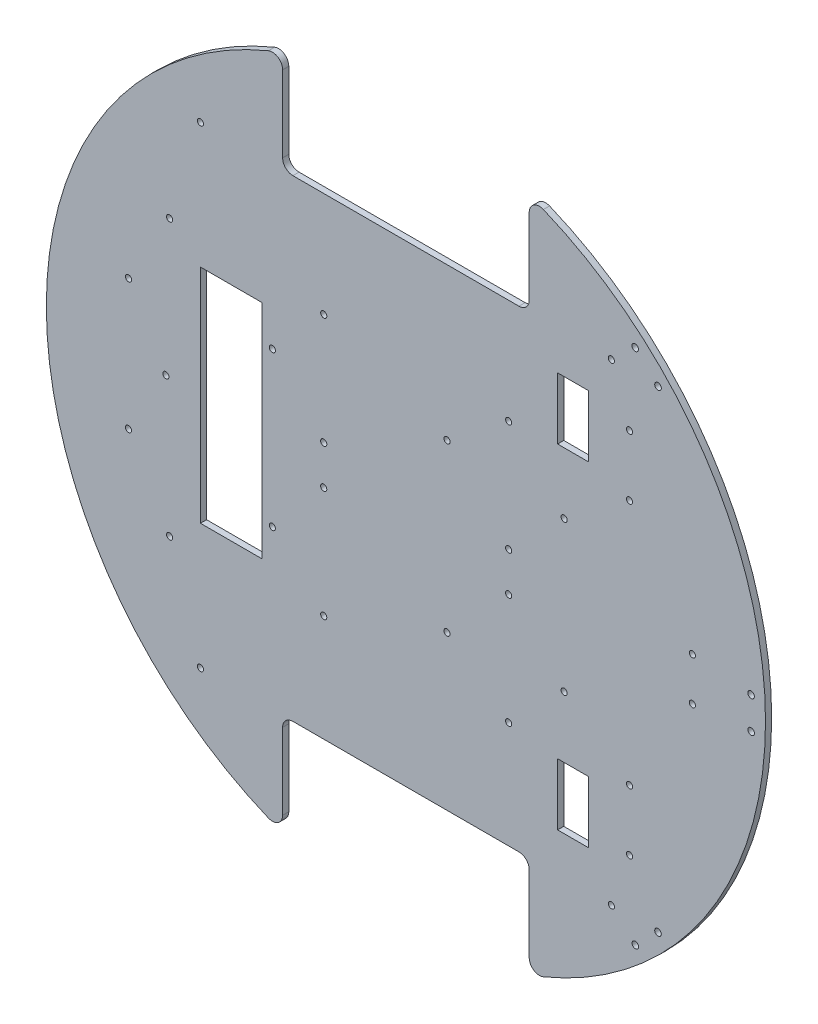
SolidWorks part; units mm, degrees
material "ｱｸﾘﾙ (中-上級の耐衝撃性)"
ref_plane "正面" through (0, 0, 0) normal (0, 0, 1) x (1, 0, 0)
ref_plane "平面" through (0, 0, 0) normal (0, 1, 0) x (1, 0, 0)
ref_plane "右側面" through (0, 0, 0) normal (1, 0, 0) x (0, 0, -1)
sketch "ｽｹｯﾁ1" plane through (0, 0, 0) normal (0, 0, 1) x (1, 0, 0)
  circle A0 centre (0, 0) radius 175
  dimension "D1" = 350
extrude "ﾎﾞｽ - 押し出し1" add sketch "ｽｹｯﾁ1" along normal blind 3
sketch "ｽｹｯﾁ2" plane through (0, 0, 3) normal (0, 0, 1) x (1, 0, 0)
  line L0 (0, 0) -> (175, 0)
  line L1 (0, 0) -> (-175, 0)
  line L2 (0, 0) -> (0, 115)
  line L3 (0, 0) -> (0, -115)
  line L4 (0, 115) -> (60, 115)
  line L5 (0, 115) -> (0, 175)
  line L6 (0, 175) -> (60, 175)
  line L7 (60, 115) -> (60, 175)
  line L8 (0, 115) -> (-60, 115)
  line L9 (0, 115) -> (0, 175)
  line L10 (0, 175) -> (-60, 175)
  line L11 (-60, 115) -> (-60, 175)
  line L13 (0, -115) -> (60, -115)
  line L14 (0, -115) -> (0, -175)
  line L15 (0, -175) -> (60, -175)
  line L16 (60, -115) -> (60, -175)
  line L17 (0, -115) -> (-60, -115)
  line L18 (0, -115) -> (0, -175)
  line L19 (0, -175) -> (-60, -175)
  line L20 (-60, -115) -> (-60, -175)
  circle A0 centre (0, 0) radius 175 construction
  circle M1 centre (0, 0) radius 175
  dimension "D1" = 115
  dimension "D2" = 60
  dimension "D3" = 60
  dimension "D4" = 60
  dimension "D5" = 115
  dimension "D6" = 60
extrude "ｶｯﾄ - 押し出し1" cut sketch "ｽｹｯﾁ2" against normal blind 3 contours L11 L8 L5 M1 | L4 L7 L5 M1 | L17 L20 L14 M1 | L16 L13 L14 M1
fillet "ﾌｨﾚｯﾄ1" radius 5 1 edges at (-60, 164.3928, 1.5)
fillet "ﾌｨﾚｯﾄ2" radius 5 3 edges at (60, 115, 1.5) (60, 164.3928, 1.5) (-60, 115, 1.5)
fillet "ﾌｨﾚｯﾄ3" radius 5 4 edges at (-60, -164.3928, 1.5) (-60, -115, 1.5) (60, -164.3928, 1.5) (60, -115, 1.5)
sketch "ｽｹｯﾁ5" plane through (0, 0, 3) normal (0, 0, 1) x (1, 0, 0)
  line L0 (0, 115) -> (-100, 115)
  line L1 (55, 115) -> (-55, 115) construction
  line L2 (0, 115) -> (100, 115)
  line L3 (0, -115) -> (100, -115)
  line L4 (55, -115) -> (-55, -115) construction
  line L5 (100, -115) -> (-100, -115)
  circle A0 centre (-100, -115) radius 1.5
  circle A1 centre (100, -115) radius 1.5
  circle A2 centre (100, 115) radius 1.5
  circle A3 centre (-100, 115) radius 1.5
  dimension "D3" = 3
  dimension "D4" = 3
  dimension "D5" = 3
  dimension "D6" = 3
  dimension "D1" = 100
  dimension "D2" = 100
extrude "ｶｯﾄ - 押し出し4" cut sketch "ｽｹｯﾁ5" against normal blind 3 contours A1 | A0 | A3 | A2
sketch "ｽｹｯﾁ7" plane through (0, 0, 3) normal (0, 0, 1) x (1, 0, 0)
  line L2 (-70, -54) -> (-100, -54)
  line L3 (-70, -54) -> (-70, 54)
  line L4 (-70, 54) -> (-100, 54)
  line L5 (-100, -54) -> (-100, 54)
  dimension "D1" = 108
  dimension "D3" = 30
extrude "ｶｯﾄ - 押し出し6" cut sketch "ｽｹｯﾁ7" against normal blind 3 contours L5 L2 L3 L4
sketch "ｽｹｯﾁ8" plane through (0, 0, 3) normal (0, 0, 1) x (1, 0, 0)
  line L0 (-100, 0) -> (-115, 0)
  line L1 (-100, -54) -> (-100, 54) construction
  line L2 (-115, 0) -> (-115, 67)
  line L3 (-115, 0) -> (-115, -67)
  circle A0 centre (-115, -67) radius 1.5
  circle A1 centre (-116.8225, 0) radius 1.5
  circle A2 centre (-115, 67) radius 1.5
  dimension "D4" = 3
  dimension "D5" = 3
  dimension "D6" = 3
  dimension "D7" = 134
  dimension "D1" = 15
  dimension "D2" = 16.8225
  dimension "D3" = 67
extrude "ｶｯﾄ - 押し出し7" cut sketch "ｽｹｯﾁ8" against normal blind 3 contours A2 | A1 | A0
sketch "ｽｹｯﾁ9" plane through (0, 0, 3) normal (0, 0, 1) x (1, 0, 0)
  line L0 (-70, 0) -> (-65, 0)
  line L1 (-70, -54) -> (-70, 54) construction
  line L2 (-65, 0) -> (-65, 37)
  line L3 (-65, 37) -> (-64.7716, 37.1905)
  line L4 (-65, 0) -> (-65, -38)
  line L5 (-65, 0) -> (20, 0)
  line L6 (20, 0) -> (20, 41)
  line L7 (20, 0) -> (20, -40)
  circle A0 centre (-65, 37) radius 1.5
  circle A1 centre (20, 41) radius 1.5
  circle A2 centre (-65, -38) radius 1.5
  circle A3 centre (20, -40) radius 1.5
  dimension "D7" = 3
  dimension "D8" = 3
  dimension "D9" = 3
  dimension "D10" = 3
  dimension "D1" = 5
  dimension "D2" = 37
  dimension "D3" = 38
  dimension "D4" = 85
  dimension "D5" = 41
  dimension "D6" = 40
extrude "ｶｯﾄ - 押し出し8" cut sketch "ｽｹｯﾁ9" against normal blind 10 contours A0 | A2 | A1 | A3
sketch "ｽｹｯﾁ10" plane through (0, 0, 3) normal (0, 0, 1) x (1, 0, 0)
  line L0 (0, 0) -> (152.2366, 0)
  line L1 (0, 0) -> (66.9742, 68.8711)
  line L2 (0, 0) -> (76.2283, -78.3873)
  line L3 (175, 0) -> (168, 0)
  line L4 (-175, 0) -> (-168, 0)
  line L5 (66.9742, 68.8711) -> (117.1237, 120.441)
  line L6 (76.2283, -78.3873) -> (117.1237, -120.441)
  line L7 (117.1237, -120.441) -> (122.6798, -115.038)
  line L8 (117.1237, -120.441) -> (111.6437, -125.9211)
  line L9 (168, 0) -> (168, 7.75)
  line L10 (168, 0) -> (168, -7.75)
  line L11 (117.1237, 120.441) -> (111.5677, 125.844)
  line L12 (117.1237, 120.441) -> (122.6798, 115.038)
  arc A0 (66.9118, -161.7029) -> (66.9118, 161.7029) centre (0, 0) ccw construction
  arc A1 (-66.9118, 161.7029) -> (-66.9118, -161.7029) centre (0, 0) ccw construction
  circle A2 centre (0, 0) radius 168
  circle A3 centre (111.6437, -125.9211) radius 1.6
  circle A4 centre (122.6798, -115.038) radius 1.6
  circle A5 centre (168, 7.75) radius 1.6
  circle A6 centre (168, -7.75) radius 1.6
  circle A7 centre (111.5677, 125.844) radius 1.6
  circle A8 centre (122.6798, 115.038) radius 1.6
  dimension "D7" = 3.2
  dimension "D8" = 3.2
  dimension "D11" = 3.2
  dimension "D12" = 3.2
  dimension "D15" = 3.2
  dimension "D16" = 3.2
  dimension "D1" = 45.8
  dimension "D2" = 45.8
  dimension "D3" = 7
  dimension "D4" = 7
  dimension "D5" = 7.75
  dimension "D6" = 7.75
  dimension "D9" = 7.75
  dimension "D10" = 7.75
  dimension "D13" = 7.75
  dimension "D14" = 7.75
extrude "ｶｯﾄ - 押し出し9" cut sketch "ｽｹｯﾁ10" against normal blind 3 contours A3 | A4 | A6 | A5 | A7 | A8
sketch "ｽｹｯﾁ11" plane through (0, 0, 3) normal (0, 0, 1) x (1, 0, 0)
  line L0 (0, 0) -> (115, 0)
  line L1 (0, 0) -> (81.3173, 81.3173)
  line L2 (0, 0) -> (81.3173, -81.3173)
  line L4 (73.8173, 96.3173) -> (88.8173, 96.3173)
  line L5 (73.8173, 96.3173) -> (73.8173, 66.3173)
  line L6 (73.8173, 66.3173) -> (88.8173, 66.3173)
  line L7 (88.8173, 96.3173) -> (88.8173, 66.3173)
  line L8 (73.8173, 96.3173) -> (88.8173, 66.3173) construction
  line L9 (73.8173, 66.3173) -> (88.8173, 96.3173) construction
  line L10 (73.8173, -66.3173) -> (88.8173, -66.3173)
  line L11 (73.8173, -66.3173) -> (73.8173, -96.3173)
  line L12 (73.8173, -96.3173) -> (88.8173, -96.3173)
  line L13 (88.8173, -66.3173) -> (88.8173, -96.3173)
  line L14 (73.8173, -66.3173) -> (88.8173, -96.3173) construction
  line L15 (73.8173, -96.3173) -> (88.8173, -66.3173) construction
  circle A0 centre (0, 0) radius 115
  dimension "D1" = 230
  dimension "D2" = 45
  dimension "D3" = 45
  dimension "D4" = 30
  dimension "D5" = 15
  dimension "D6" = 15
  dimension "D7" = 30
extrude "ｶｯﾄ - 押し出し10" cut sketch "ｽｹｯﾁ11" against normal blind 10 contours L7 L6 L5 L4 | L13 L12 L11 L10
sketch "ｽｹｯﾁ12" plane through (0, 0, 3) normal (0, 0, 1) x (1, 0, 0)
  circle A3 centre (139.4, 10.5) radius 1.5
  circle A4 centre (139.4, -10.5) radius 1.5
  dimension "D4" = 3
  dimension "D1" = 21
extrude "ｶｯﾄ - 押し出し11" cut sketch "ｽｹｯﾁ12" against normal through all
sketch "ｽｹｯﾁ13" plane through (0, 0, 3) normal (0, 0, 1) x (1, 0, 0)
  line L0 (175, 0) -> (-70, 0) construction
  line L1 (-70, -54) -> (-70, 54) construction
  line L2 (50, 62.5) -> (50, 11.5) construction
  arc A0 (66.9118, -161.7029) -> (66.9118, 161.7029) centre (0, 0) ccw construction
  circle A1 centre (50, 10) radius 1.5
  circle A2 centre (50, 64) radius 1.5
  circle A3 centre (-40, 64) radius 1.5
  circle A4 centre (-40, 10) radius 1.5
  circle A5 centre (77, 36.5) radius 1.5
  dimension "D1" = 3
  dimension "D2" = 10
  dimension "D3" = 3
  dimension "D4" = 54
  dimension "D5" = 3
  dimension "D6" = 3
  dimension "D7" = 27
  dimension "D8" = 3
  dimension "D9" = 90
  dimension "D10" = 90
  dimension "D11" = 26.5
  dimension "D12" = 54
extrude "ｶｯﾄ - 押し出し12" cut sketch "ｽｹｯﾁ13" against normal through all
pattern_linear "直線ﾊﾟﾀｰﾝ1" count 2 spacing 73 along (0, -1, 0) of "ｶｯﾄ - 押し出し12"
sketch "ｽｹｯﾁ14" plane through (0, 0, 3) normal (0, 0, 1) x (1, 0, 0)
  line L0 (175, 0) -> (98.9957, 0) construction
  arc A0 (66.9118, -161.7029) -> (66.9118, 161.7029) centre (0, 0) ccw construction
  circle A1 centre (108.8173, 89.5) radius 1.5
  circle A2 centre (108.8173, 60) radius 1.5
  dimension "D1" = 60
  dimension "D2" = 3
  dimension "D3" = 3
  dimension "D4" = 29.5
extrude "ｶｯﾄ - 押し出し14" cut sketch "ｽｹｯﾁ14" against normal through all
sketch "ｽｹｯﾁ17" plane through (0, 0, 3) normal (0, 0, 1) x (1, 0, 0)
  circle A2 centre (108.8173, -60) radius 1.5
  circle A3 centre (108.8173, -89.5) radius 1.5
  dimension "D2" = 3
  dimension "D3" = 3
  dimension "D4" = 29.5
extrude "ｶｯﾄ - 押し出し15" cut sketch "ｽｹｯﾁ17" against normal through all
sketch "ｽｹｯﾁ18" plane through (0, 0, 3) normal (0, 0, 1) x (1, 0, 0)
  line L0 (-100, -54) -> (-100, 54) construction
  circle A0 centre (-135, 31.75) radius 1.5
  circle A1 centre (-135, -31.75) radius 1.5
  dimension "D3" = 3
  dimension "D4" = 3
  dimension "D5" = 63.5
  dimension "D1" = 35
  dimension "D2" = 35
extrude "ｶｯﾄ - 押し出し16" cut sketch "ｽｹｯﾁ18" against normal through all
sketch "ｽｹｯﾁ22" plane through (0, 0, 3) normal (0, 0, 1) x (1, 0, 0)
  point P0 (0, 0)
